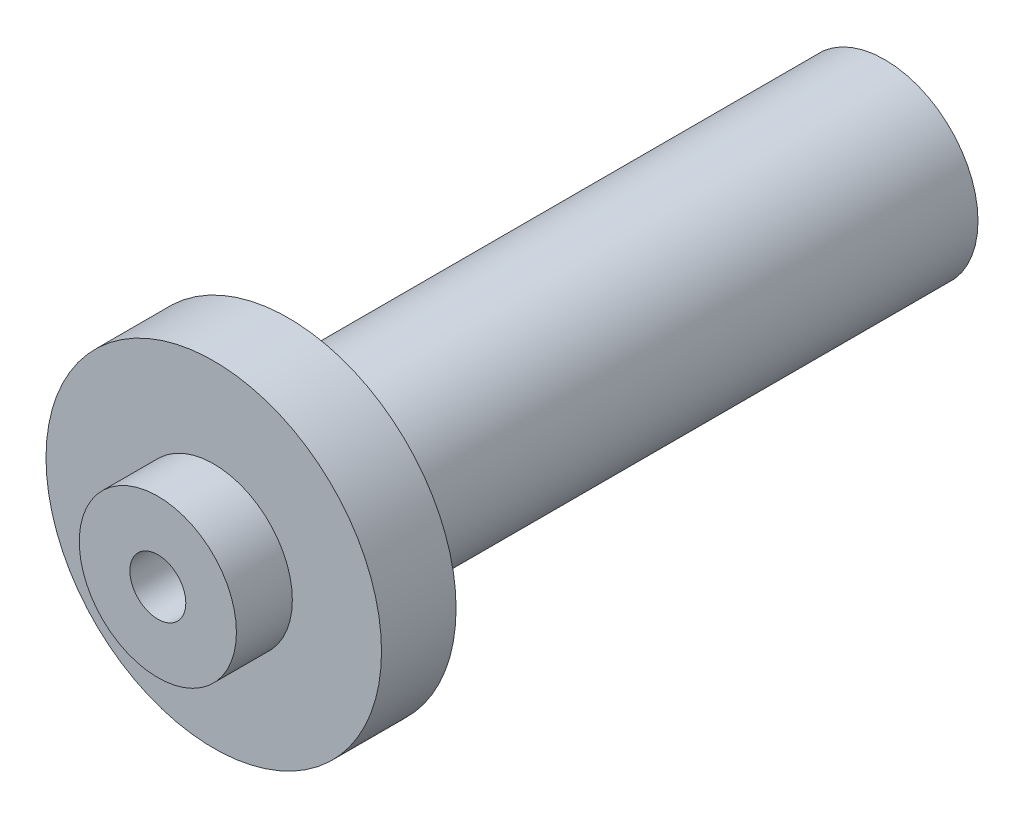
SolidWorks part; units mm, degrees
ref_plane "Front Plane" through (0, 0, 0) normal (0, 0, 1) x (1, 0, 0)
ref_plane "Top Plane" through (0, 0, 0) normal (0, 1, 0) x (1, 0, 0)
ref_plane "Right Plane" through (0, 0, 0) normal (1, 0, 0) x (0, 0, -1)
sketch "Sketch3" plane through (0, 0, 0) normal (0, 0, 1) x (1, 0, 0)
  circle A0 centre (0, 0) radius 31.75
extrude "Boss-Extrude1" add sketch "Sketch3" along normal blind 203.2
sketch "Sketch4" plane through (0, 0, 203.2) normal (0, 0, 1) x (1, 0, 0)
  circle A0 centre (0, 0) radius 57.15
extrude "Boss-Extrude2" add sketch "Sketch4" along normal blind 25.4
sketch "Sketch5" plane through (0, 0, 228.6) normal (0, 0, 1) x (1, 0, 0)
  circle A0 centre (0, 0) radius 26.7716
extrude "Boss-Extrude3" add sketch "Sketch5" along normal blind 19.05
sketch "Sketch6" plane through (0, 0, 247.65) normal (0, 0, 1) x (1, 0, 0)
  circle A0 centre (0, 0) radius 9.525
extrude "Cut-Extrude1" cut sketch "Sketch6" against normal through all
